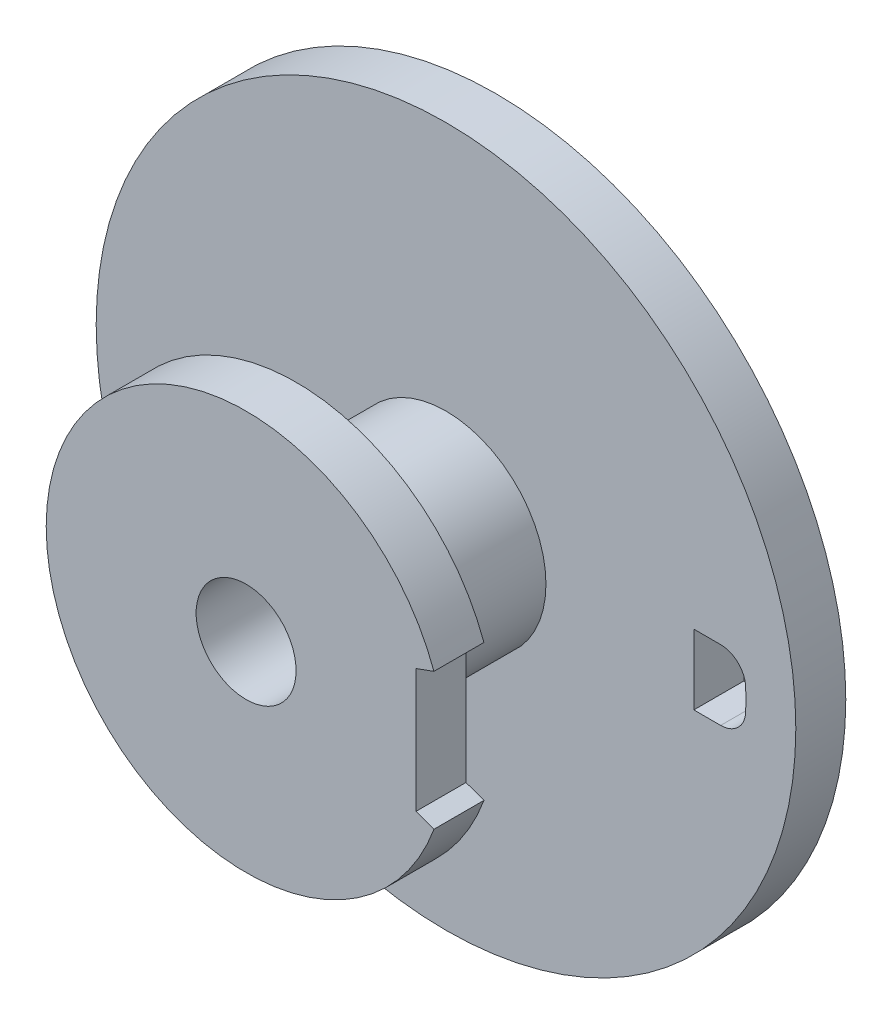
SolidWorks part; units mm, degrees
ref_plane "Alzado" through (0, 0, 0) normal (0, 0, 1) x (1, 0, 0)
ref_plane "Planta" through (0, 0, 0) normal (0, 1, 0) x (1, 0, 0)
ref_plane "Vista lateral" through (0, 0, 0) normal (1, 0, 0) x (0, 0, -1)
sketch "Croquis1" plane through (0, 0, 0) normal (0, 0, 1) x (1, 0, 0)
  circle A0 centre (0, 0) radius 0.5
  circle A1 centre (0, 0) radius 0.25
  dimension "D1" = 1
  dimension "D2" = 0.5
extrude "Saliente-Extruir1" add sketch "Croquis1" against normal blind 0.75
sketch "Croquis2" plane through (0, 0, 0) normal (0, 0, 1) x (1, 0, 0)
  line L0 (0.85, 0.3094) -> (0, 0) construction
  line L1 (0, 0) -> (0.85, -0.3094) construction
  line L4 (0, 0) -> (0.7035, 0) construction
  line L5 (0.85, 0.3094) -> (0.85, -0.3094)
  line L8 (0.85, 0.3094) -> (0.9397, 0.342)
  line L9 (0.85, -0.3094) -> (0.9397, -0.342)
  arc A0 (0.342, -0.9397) -> (0.9397, -0.342) centre (0, 0) ccw
  circle A1 centre (0, 0) radius 0.25 construction
  circle A2 centre (0, 0) radius 0.25
  arc A3 (0.9397, 0.342) -> (0.342, -0.9397) centre (0, 0) ccw
  dimension "D1" = 2
  dimension "D2" = 20
  dimension "D3" = 20
  dimension "D5" = 0.85
extrude "Saliente-Extruir2" add sketch "Croquis2" along normal blind 0.25
sketch "Croquis3" plane through (0, 0, -0.75) normal (0, 0, -1) x (-1, 0, 0)
  circle A0 centre (0, 0) radius 1.75
  circle A1 centre (0, 0) radius 0.25 construction
  circle A2 centre (0, 0) radius 0.25
  dimension "D1" = 3.5
extrude "Saliente-Extruir3" add sketch "Croquis3" along normal blind 0.25
sketch "Croquis4" plane through (0, 0, -1) normal (0, 0, -1) x (-1, 0, 0)
  line L0 (-1.3741, 0.175) -> (-1.2398, 0.175)
  line L1 (-1.2398, 0.175) -> (-1.2398, -0.175)
  line L2 (-1.2398, -0.175) -> (-1.3741, -0.175)
  arc A0 (-1.499, 0.0545) -> (-1.499, -0.0545) centre (0, 0) ccw
  arc A1 (-1.3741, -0.175) -> (-1.499, -0.0545) centre (-1.3741, -0.05) cw
  arc A2 (-1.3741, 0.175) -> (-1.499, 0.0545) centre (-1.3741, 0.05) ccw
  point P1 (-1.2398, 0)
  point P11 (-1.4898, 0.175)
  dimension "D1" = 1.5
  dimension "D2" = 0.35
  dimension "D3" = 0.25
  dimension "D4" = 0.125
extrude "Cortar-Extruir1" cut sketch "Croquis4" against normal up to next
